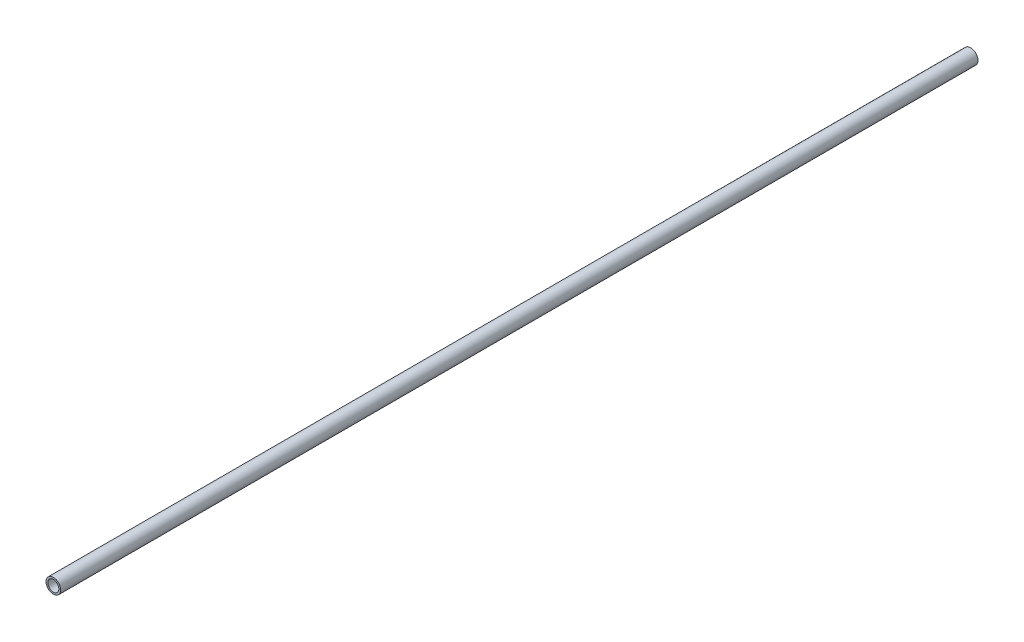
SolidWorks part; units mm, degrees
material "carbon fiber"
ref_plane "Front Plane" through (0, 0, 0) normal (0, 0, 1) x (1, 0, 0)
ref_plane "Top Plane" through (0, 0, 0) normal (0, 1, 0) x (1, 0, 0)
ref_plane "Right Plane" through (0, 0, 0) normal (1, 0, 0) x (0, 0, -1)
sketch "Эскиз1" plane through (0, 0, 0) normal (0, 0, 1) x (1, 0, 0)
  circle A0 centre (0, 0) radius 4
  circle A1 centre (0, 0) radius 3
  dimension "D1" = 8
  dimension "D2" = 1
extrude "Бобышка-Вытянуть1" add sketch "Эскиз1" along normal mid plane 500
